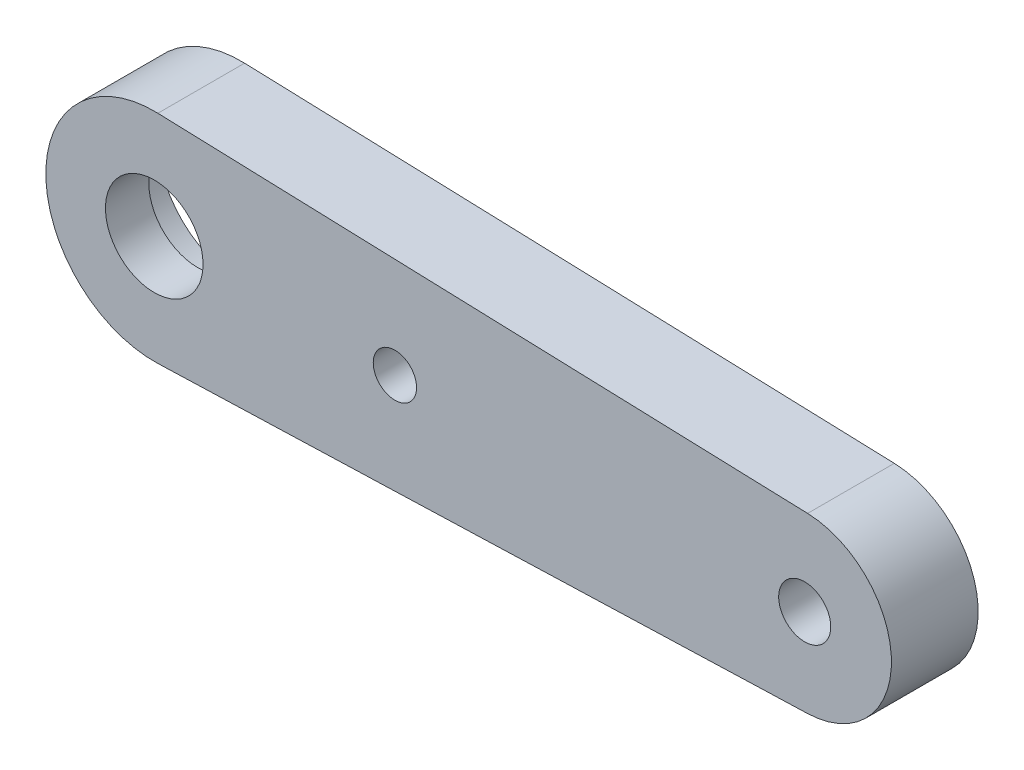
SolidWorks part; units mm, degrees
ref_plane "Front Plane" through (0, 0, 0) normal (0, 0, 1) x (1, 0, 0)
ref_plane "Top Plane" through (0, 0, 0) normal (0, 1, 0) x (1, 0, 0)
ref_plane "Right Plane" through (0, 0, 0) normal (1, 0, 0) x (0, 0, -1)
sketch "Sketch14" plane through (0, 0, 0) normal (0, 0, 1) x (1, 0, 0)
  line L0 (0.1667, 4.9972) -> (30.1333, 3.9978)
  line L1 (0.1667, -4.9972) -> (30.1333, -3.9978)
  circle A0 centre (0, 0) radius 1.2
  circle A1 centre (0, 0) radius 5
  circle A2 centre (30, 0) radius 1.2
  circle A3 centre (30, 0) radius 4
  dimension "D1" = 2.4
  dimension "D2" = 10
  dimension "D3" = 8
  dimension "D4" = 30
extrude "Boss-Extrude1" add sketch "Sketch14" along normal blind 4 separate body contours A3 L0 A1 L1 | A3 A2 | A1 A0
sketch "Sketch15" plane through (0, 0, 4) normal (0, 0, 1) x (1, 0, 0)
  line L0 (0.3632, -3.8328) -> (16.1217, -2.3395)
  line L1 (0.3632, 3.8328) -> (16.1217, 2.3395)
  circle A0 centre (0, 0) radius 3.85
  circle A1 centre (15.9, 0) radius 2.35
  line M5 (30.1333, 3.9978) -> (0.1667, 4.9972)
  circle M7 centre (0, 0) radius 1.2
  dimension "D1" = 7.7
  dimension "D3" = 4.7
  dimension "D2" = 15.9
extrude "Cut-Extrude1" cut sketch "Sketch15" against normal up to surface (1.5 mm away) from offset 2.5 contours A1 L1 A0 L0 | A0 M7 | A1 M5 offset against normal yes
sketch "Sketch16" plane through (0, 0, 1.5) normal (0, 0, -1) x (-1, 0, 0)
  line L1 (0, 3.85) -> (-6, 3.85)
  line L2 (0, 3.85) -> (0, -3.85)
  line L3 (0, -3.85) -> (-6, -3.85)
  line L4 (-6, 3.85) -> (-6, -3.85)
  circle A0 centre (0, 0) radius 3.85
  point P8 (0, 0)
  line M2 (-16.1217, -2.3395) -> (-0.3632, -3.8328)
  arc M3 (-0.3632, -3.8328) -> (-0.3632, 3.8328) centre (0, 0) ccw
  line M4 (-0.3632, 3.8328) -> (-16.1217, 2.3395)
  circle M6 centre (0, 0) radius 1.2
  dimension "D1" = 7.7
  dimension "D2" = 6
extrude "Cut-Extrude2" cut sketch "Sketch16" against normal blind 0.5 contours A0 L4 M4 M2 | A0 L2 M3 M6 | L2 M3 M6
sketch "Sketch17" plane through (0, 0, 1.5) normal (0, 0, -1) x (-1, 0, 0)
  circle A0 centre (-11.1, 0) radius 1
  dimension "D1" = 2
  dimension "D2" = 11.1
extrude "Cut-Extrude3" cut sketch "Sketch17" against normal blind 6
sketch "Sketch18" plane through (0, 0, 4) normal (0, 0, 1) x (1, 0, 0)
  circle A0 centre (0, 0) radius 2.25
  dimension "D1" = 4.5
extrude "Cut-Extrude4" cut sketch "Sketch18" against normal blind 10
